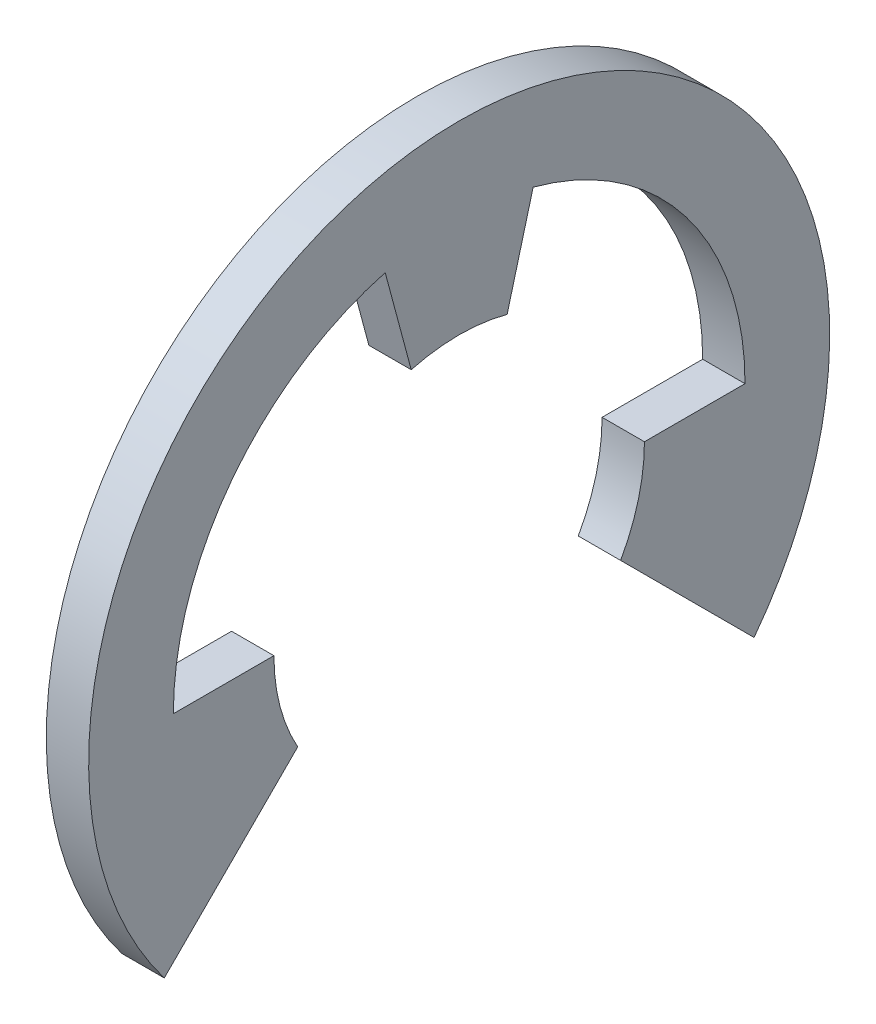
SolidWorks part; units mm, degrees
ref_plane "Front Plane" through (0, 0, 0) normal (0, 0, 1) x (1, 0, 0)
ref_plane "Top Plane" through (0, 0, 0) normal (0, 1, 0) x (1, 0, 0)
ref_plane "Right Plane" through (0, 0, 0) normal (1, 0, 0) x (0, 0, -1)
sketch "Sketch1" plane through (0, 0, 0) normal (1, 0, 0) x (0, 0, -1)
  line L0 (-3.5, 0) -> (-5.4, 0)
  line L1 (-0.9059, 3.3807) -> (-1.3976, 5.216)
  line L2 (3.5, 0) -> (5.4, 0)
  line L3 (1.3976, 5.216) -> (0.9059, 3.3807)
  line L4 (-3.05, -1.7168) -> (-5.5712, -4.2381)
  line L5 (3.05, -1.7168) -> (5.5712, -4.2381)
  line L9 (0, 0) -> (0, 7) construction
  arc A0 (-3.5, 0) -> (-3.05, -1.7168) centre (0, 0) ccw
  arc A1 (5.5712, -4.2381) -> (-5.5712, -4.2381) centre (0, 0) ccw
  arc A2 (5.4, 0) -> (1.3976, 5.216) centre (0, 0) ccw
  arc A3 (0.9059, 3.3807) -> (-0.9059, 3.3807) centre (0, 0) ccw
  arc A4 (-1.3976, 5.216) -> (-5.4, 0) centre (0, 0) ccw
  arc A5 (3.05, -1.7168) -> (3.5, 0) centre (0, 0) ccw
  circle A6 centre (0, 0) radius 3.5 construction
  dimension "D1" = 30
  dimension "D2" = 90
  dimension "REE_D" = 14
  dimension "REE_D_s" = 7
  dimension "REE_B_s" = 1.6
  dimension "REE_H" = 6.1
extrude "Boss-Extrude1" add sketch "Sketch1" along normal blind 0.8
